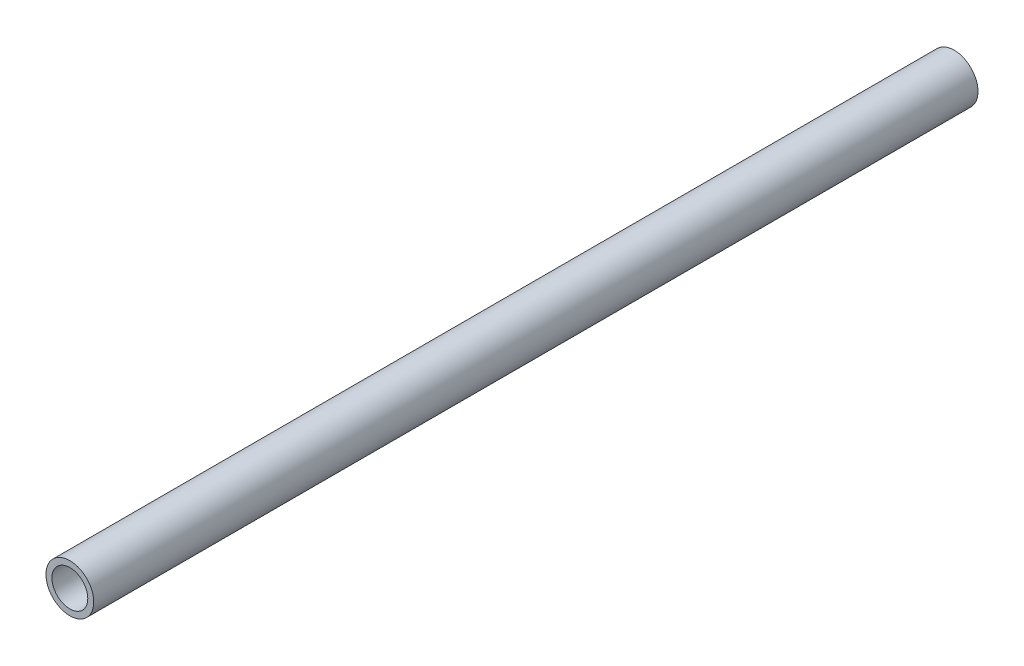
SolidWorks part; units mm, degrees
material "6061-T6 (SS)"
ref_plane "Plan de face" through (0, 0, 0) normal (0, 0, 1) x (1, 0, 0)
ref_plane "Plan de dessus" through (0, 0, 0) normal (0, 1, 0) x (1, 0, 0)
ref_plane "Plan de droite" through (0, 0, 0) normal (1, 0, 0) x (0, 0, -1)
sketch "Esquisse1" plane through (0, 0, 0) normal (0, 0, 1) x (1, 0, 0)
  circle A0 centre (0, 0) radius 12.7
  circle A1 centre (0, 0) radius 9.525
  dimension "D1" = 3.175
  dimension "D2" = 25.4
extrude "Boss.-Extru.1" add sketch "Esquisse1" along normal blind 469.9
